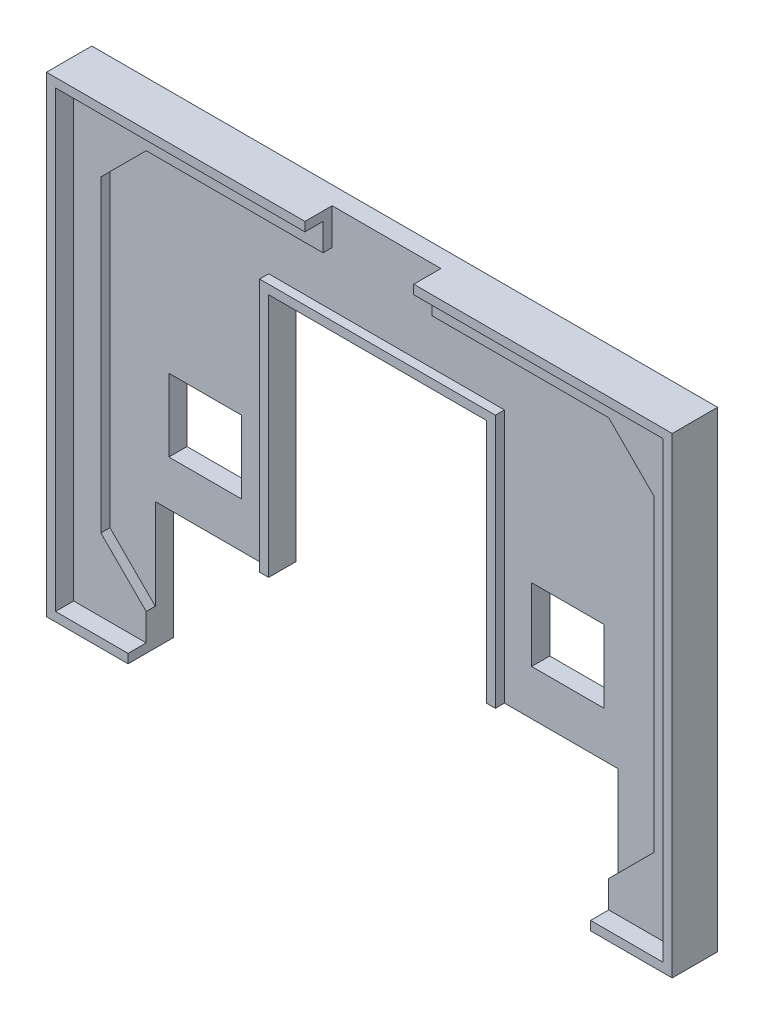
SolidWorks part; units mm, degrees
ref_plane "Přední rovina" through (0, 0, 0) normal (0, 0, 1) x (1, 0, 0)
ref_plane "Horní rovina" through (0, 0, 0) normal (0, 1, 0) x (1, 0, 0)
ref_plane "Pravá rovina" through (0, 0, 0) normal (1, 0, 0) x (0, 0, -1)
sketch "Skica1" plane through (0, 0, 0) normal (0, 0, 1) x (1, 0, 0)
  line L1 (-33.5, -25) -> (33.5, -25)
  line L2 (-33.5, -25) -> (-33.5, 25)
  line L3 (-33.5, 25) -> (33.5, 25)
  line L4 (33.5, -25) -> (33.5, 25)
  line L5 (-33.5, -25) -> (33.5, 25) construction
  line L6 (-33.5, 25) -> (33.5, -25) construction
  point P0 (0, 0)
  dimension "D1" = 67
  dimension "D2" = 50
extrude "Přidat vysunutím1" add sketch "Skica1" along normal blind 3
sketch "Skica2" plane through (0, 0, 3) normal (0, 0, 1) x (1, 0, 0)
  line L0 (-1000, 0) -> (49000, 0) construction
  line L1 (0, -1000) -> (0, 49000) construction
  line L2 (-1000, -22) -> (49000, -22) construction
  line L3 (-25.5, -1000) -> (-25.5, 49000) construction
  line L4 (-30.5, -1000) -> (-30.5, 49000) construction
  line L6 (-33.5, -25) -> (33.5, -25) construction
  line L7 (-25.5, -22) -> (-30.5, -17)
  line L8 (-30.5, -17) -> (-30.5, 17)
  line L9 (-25.5, -22) -> (25.5, -22)
  line L10 (30.5, -17) -> (30.5, 17)
  line L11 (25.5, -22) -> (30.5, -17)
  line L12 (25.5, 22) -> (30.5, 17)
  line L13 (-25.5, 22) -> (25.5, 22)
  line L14 (-25.5, 22) -> (-30.5, 17)
  point P20 (0, -22)
  point P21 (30.5, 0)
  point P24 (-30.5, 0)
  dimension "D1" = 30.5
  dimension "D2" = 5
  dimension "D3" = 3
  dimension "D4" = 45
extrude "Odebrat vysunutím1" cut sketch "Skica2" against normal offset from surface (1 mm away) 2 up to face at (0, 0, 0)
sketch "Skica3" plane through (0, 0, 0) normal (0, 0, -1) x (-1, 0, 0)
  line L0 (0, -1000) -> (0, 49000) construction
  line L1 (33.5, -25) -> (-33.5, -25) construction
  line L2 (24, 1) -> (16, 1)
  line L3 (24, 1) -> (24, -7)
  line L4 (24, -7) -> (16, -7)
  line L5 (16, 1) -> (16, -7)
  line L6 (-16, 1) -> (-16, -7)
  line L7 (33.5, -25) -> (-33.5, -25) construction
  line L8 (25.5, -25) -> (-25.5, -25)
  line L9 (25.5, -25) -> (25.5, -12)
  line L11 (-25.5, -25) -> (-25.5, -12)
  line L12 (-24, -7) -> (-16, -7)
  line L13 (25.5, -12) -> (12, -12)
  line L15 (12, -12) -> (12, 15)
  line L16 (12, 15) -> (-12, 15)
  line L17 (-12, -12) -> (-12, 15)
  line L18 (-12, -12) -> (-25.5, -12)
  line L19 (-24, 1) -> (-24, -7)
  line L20 (-24, 1) -> (-16, 1)
  dimension "D1" = 16
  dimension "D2" = 8
  dimension "D3" = 18
  dimension "D4" = 13
  dimension "D5" = 51
  dimension "D6" = 24
  dimension "D7" = 27
extrude "Odebrat vysunutím2" cut sketch "Skica3" against normal through all
sketch "Skica4" plane through (0, 0, 2) normal (0, 0, 1) x (1, 0, 0)
  line L0 (12, 15) -> (12, -12) construction
  line L1 (-12, -12) -> (-12, 15) construction
  line L2 (-12, 15) -> (12, 15) construction
  line L3 (12, 15) -> (12, -12)
  line L4 (-12, -12) -> (-12, 15)
  line L5 (-12, 15) -> (12, 15)
extrude "Vysunout tenkostěnný1" add sketch "Skica4" along normal up to surface (1 mm away) thin up to face at (0, -3.5714, 3) thin type one direction reverse wall 1
sketch "Skica5" plane through (0, 0, 0) normal (0, 0, -1) x (-1, 0, 0)
  line L0 (-33.5, 25) -> (33.5, 25) construction
  line L1 (33.5, 25) -> (33.5, -25) construction
  line L2 (33.5, -25) -> (25.5, -25) construction
  line L3 (-33.5, -25) -> (-33.5, 25) construction
  line L4 (-25.5, -25) -> (-33.5, -25) construction
  line L5 (-33.5, 25) -> (33.5, 25)
  line L6 (33.5, 25) -> (33.5, -25)
  line L7 (33.5, -25) -> (25.5, -25)
  line L8 (-33.5, -25) -> (-33.5, 25)
  line L9 (-25.5, -25) -> (-33.5, -25)
extrude "Vysunout tenkostěnný2" add sketch "Skica5" against normal blind 5 thin thin type one direction reverse wall 1
sketch "Skica6" plane through (0, 0, 2) normal (0, 0, 1) x (1, 0, 0)
  line L0 (0, -1000) -> (0, 49000) construction
  line L1 (25.5, 22) -> (-25.5, 22) construction
  line L2 (-6, 22) -> (6, 22)
  line L3 (-6, 22) -> (-6, 26)
  line L4 (-6, 26) -> (6, 26)
  line L5 (6, 22) -> (6, 26)
  line L6 (34.5, 26) -> (-34.5, 26) construction
  dimension "D1" = 12
extrude "Odebrat vysunutím3" cut sketch "Skica6" along normal through all
sketch "Skica7" plane through (0, 0, 0) normal (0, 0, -1) x (-1, 0, 0)
  line L0 (-412.4785, -204.4844) -> (-71.1451, -204.4844) construction
  line L1 (-32.44, 14.5405) -> (-23.4595, 23.94)
  line L2 (-23.4595, 23.94) -> (-14.06, 14.9595)
  line L3 (-14.06, 14.9595) -> (-23.0405, 5.56)
  line L4 (-23.0405, 5.56) -> (-32.44, 14.5405)
  line L5 (-34.5, 26) -> (34.5, 26) construction
  line L6 (0, 0) -> (0, 28.27) construction
  line L7 (-34.5, -26) -> (-34.5, 26) construction
  line L8 (14.06, 14.9595) -> (23.0405, 5.56)
  line L9 (23.4595, 23.94) -> (14.06, 14.9595)
  line L10 (32.44, 14.5405) -> (23.4595, 23.94)
  line L11 (23.0405, 5.56) -> (32.44, 14.5405)
  dimension "D1" = 13
  dimension "D2" = 13
  dimension "D3" = 2.06
  dimension "D4" = 2.06
  dimension "D5" = 2.06
extrude "Odebrat vysunutím5" cut sketch "Skica7" against normal blind 1
sketch "Skica8" plane through (0, 0, 0) normal (0, 0, -1) x (-1, 0, 0)
  line L0 (-28.5439, 14.2757) -> (-27.8208, 13.5849)
  line L1 (-27.8208, 13.5849) -> (-26.0938, 15.3925)
  line L2 (-26.0938, 15.3925) -> (-26.8168, 16.0833)
  line L3 (-26.8168, 16.0833) -> (-28.5439, 14.2757)
  line L4 (-32.44, 14.5405) -> (-23.0405, 5.56) construction
  line L5 (-23.4595, 23.94) -> (-32.44, 14.5405) construction
  line L6 (-24.7444, 18.2524) -> (-24.0214, 17.5616)
  line L7 (-24.0214, 17.5616) -> (-22.2944, 19.3692)
  line L8 (-22.2944, 19.3692) -> (-23.0174, 20.06)
  line L9 (-23.0174, 20.06) -> (-24.7444, 18.2524)
  line L10 (-14.06, 14.9595) -> (-23.4595, 23.94) construction
  line L12 (-24.551, 9.7693) -> (-26.3586, 11.4963)
  line L13 (-23.4595, 23.94) -> (-32.44, 14.5405) construction
  line L14 (-26.3586, 11.4963) -> (-20.1414, 18.0037)
  line L15 (-20.1414, 18.0037) -> (-18.3338, 16.2767)
  line L16 (-32.44, 14.5405) -> (-23.0405, 5.56) construction
  line L17 (0, 0) -> (0, 27.7759) construction
  line L30 (-26.8168, 16.0833) -> (-27.8208, 13.5849) construction
  line L31 (-27.9498, 19.2402) -> (-18.5502, 10.2598) construction
  line L32 (-23.0405, 5.56) -> (-14.06, 14.9595) construction
  line L33 (-24.551, 9.7693) -> (-20.3298, 11.96)
  line L34 (-20.3298, 11.96) -> (-18.3338, 16.2767)
  line L35 (26.0938, 15.3925) -> (26.8168, 16.0833)
  line L36 (27.8208, 13.5849) -> (26.0938, 15.3925)
  line L37 (28.5439, 14.2757) -> (27.8208, 13.5849)
  line L38 (26.8168, 16.0833) -> (28.5439, 14.2757)
  line L39 (22.2944, 19.3692) -> (23.0174, 20.06)
  line L40 (24.0214, 17.5616) -> (22.2944, 19.3692)
  line L41 (24.7444, 18.2524) -> (24.0214, 17.5616)
  line L42 (23.0174, 20.06) -> (24.7444, 18.2524)
  line L43 (24.551, 9.7693) -> (20.3298, 11.96)
  line L44 (24.551, 9.7693) -> (26.3586, 11.4963)
  line L45 (26.3586, 11.4963) -> (20.1414, 18.0037)
  line L46 (20.1414, 18.0037) -> (18.3338, 16.2767)
  line L47 (20.3298, 11.96) -> (18.3338, 16.2767)
  point P22 (-18.7598, 19.4498)
  dimension "D1" = 1
  dimension "2,5" = 2.5
  dimension "D2" = 2.5
  dimension "D3" = 3
  dimension "D4" = 2.5
  dimension "D5" = 1
  dimension "D6" = 2.5
  dimension "D7" = 2.5
  dimension "D8" = 2.5
  dimension "D9" = 3
  dimension "D10" = 2.5
  dimension "D11" = 2.5
  dimension "D12" = 2
  dimension "D13" = 2
  dimension "D14" = 2
  dimension "D15" = 2
  dimension "D16" = 9
  dimension "D17" = 4.7558
extrude "Přidat vysunutím5" add sketch "Skica8" along normal blind 1 from offset 1 offset against normal yes
sketch "Skica9" plane through (0, 0, 0) normal (0, 0, -1) x (-1, 0, 0)
  line L0 (34.5, 26) -> (34.5, -26) construction
  line L1 (34.5, -26) -> (25.5, -26) construction
  text T0 "GRIN\r\n\r\n" font "BLOXAT" height 6
  dimension "D1" = 45.3639
  dimension "D2" = 43.3451
extrude "Odebrat vysunutím6" cut sketch "Skica9" against normal blind 1
